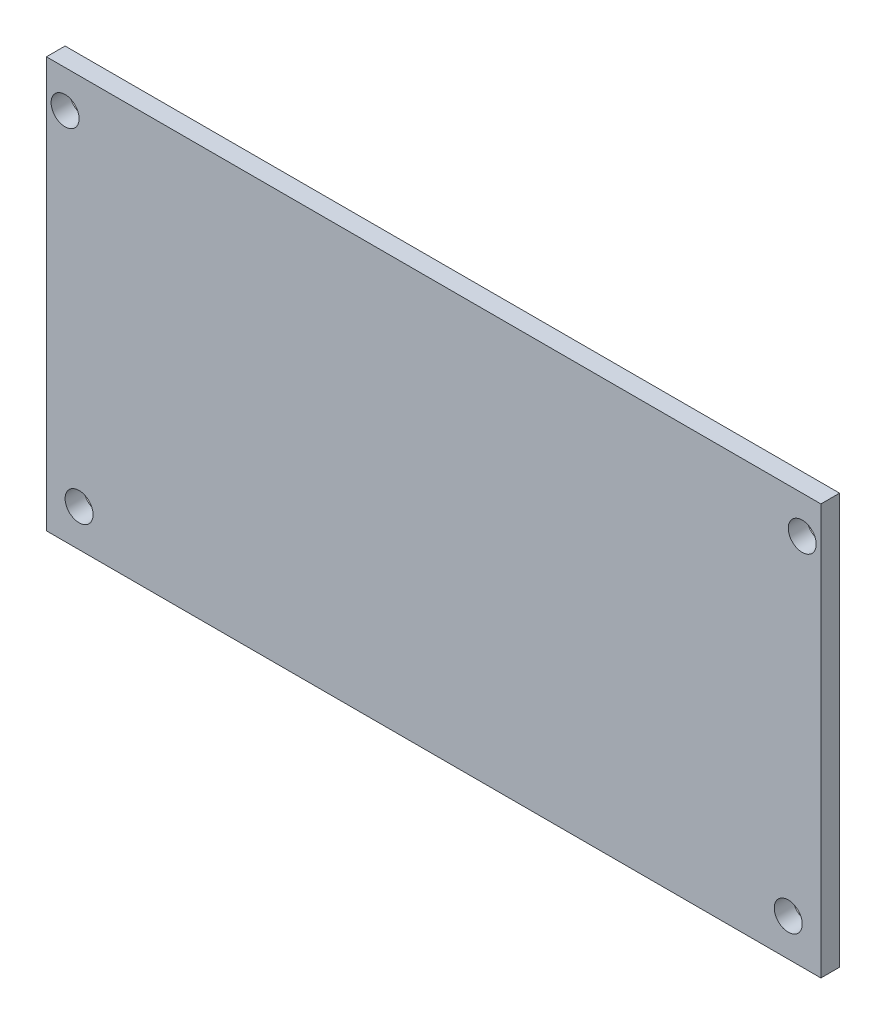
SolidWorks part; units mm, degrees
ref_plane "Plan de face" through (0, 0, 0) normal (0, 0, 1) x (1, 0, 0)
ref_plane "Plan de dessus" through (0, 0, 0) normal (0, 1, 0) x (1, 0, 0)
ref_plane "Plan de droite" through (0, 0, 0) normal (1, 0, 0) x (0, 0, -1)
sketch "Esquisse1" plane through (0, 0, 0) normal (0, 0, 1) x (1, 0, 0)
  line L1 (0, 0) -> (-83, 0)
  line L2 (0, 0) -> (0, 44)
  line L3 (0, 44) -> (-83, 44)
  line L4 (-83, 0) -> (-83, 44)
  dimension "D1" = 44
  dimension "D2" = 83
extrude "Extrusion1" add sketch "Esquisse1" along normal blind 2
sketch "Esquisse2" plane through (0, 0, 2) normal (0, 0, 1) x (1, 0, 0)
  line L0 (-41.5, 44) -> (-41.5, 40)
  line L1 (-81, 40) -> (-2, 40) construction
  line L2 (-41.5, 4) -> (-41.5, 0)
  line L3 (-79.5, 4) -> (-3.5, 4) construction
  line L4 (-83, 0) -> (0, 0) construction
  line L5 (0, 44) -> (-83, 44) construction
  circle A0 centre (-81, 40) radius 1.5
  circle A1 centre (-2, 40) radius 1.5
  circle A2 centre (-3.5, 4) radius 1.5
  circle A3 centre (-79.5, 4) radius 1.5
  dimension "D1" = 3
  dimension "D2" = 79
  dimension "D3" = 76
  dimension "D4" = 36
  dimension "D5" = 4
extrude "Enlèv. mat.-Extru.1" cut sketch "Esquisse2" against normal blind 10 contours A0 | A3 | A2 | A1
